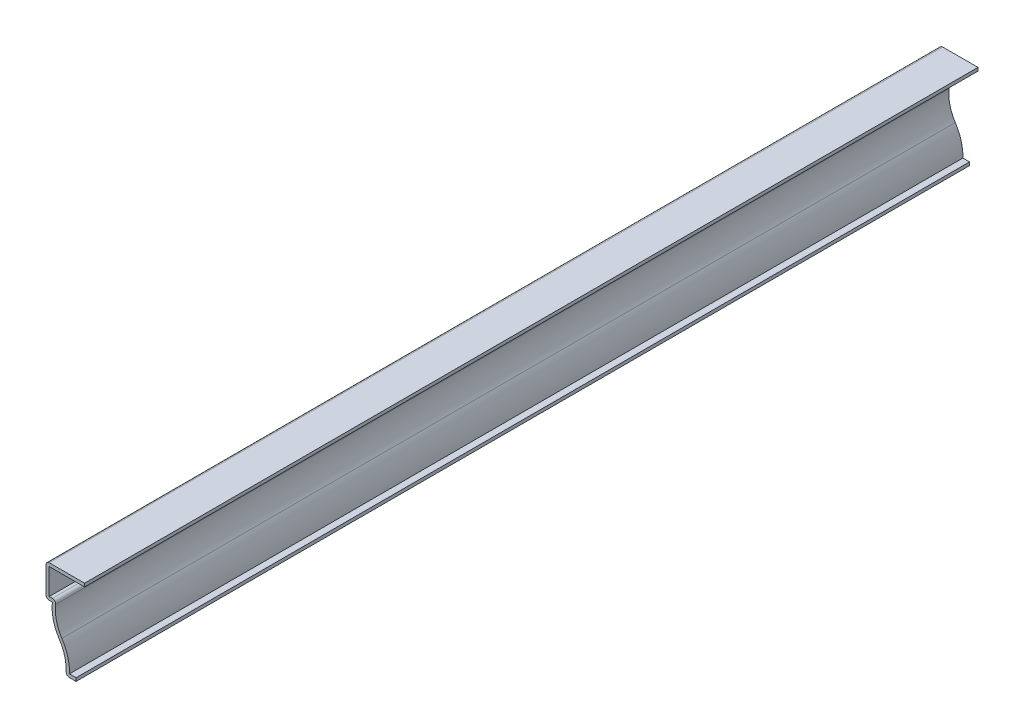
SolidWorks part; units mm, degrees
ref_plane "Front Plane" through (0, 0, 0) normal (0, 0, 1) x (1, 0, 0)
ref_plane "Top Plane" through (0, 0, 0) normal (0, 1, 0) x (1, 0, 0)
ref_plane "Right Plane" through (0, 0, 0) normal (1, 0, 0) x (0, 0, -1)
sketch "Sketch1" plane through (0, 0, 0) normal (0, 0, 1) x (1, 0, 0)
  line L0 (0, 0) -> (0, 34.925) construction
  line L1 (0, 34.925) -> (-15.0812, 34.925)
  line L2 (-15.0812, 34.925) -> (-15.0813, 22.225)
  line L3 (-15.0813, 22.225) -> (-12.5892, 22.225)
  line L4 (-7.2818, 0) -> (-3.313, 0)
  line L5 (-3.313, 0) -> (0, 0) construction
  line L6 (-13.8112, 34.925) -> (-13.8112, 22.225) construction
  line L9 (-15.0813, 22.225) -> (-15.0813, 0) construction
  line L10 (-7.2818, 0) -> (-15.0813, 0) construction
  arc A0 (-12.5892, 22.225) -> (-9.9355, 11.1125) centre (3.9688, 20.306) ccw
  arc A1 (-9.9355, 11.1125) -> (-7.2818, 0) centre (-23.8397, 1.919) cw
  point P11 (-3.313, 17.9522)
  point P12 (-13.5962, 22.225)
  point P13 (-13.8352, 22.225)
  point P15 (-15.0812, 11.1125)
  point P16 (-13.6318, 17.6418)
  point P17 (-12.7, 22.225)
  point P18 (-13.6318, 17.6442)
  point P19 (-10.4095, 11.1125)
  point P20 (-28.3255, 4.309)
  point P21 (-10.0473, 12.6765)
  point P22 (0, 0)
  point P23 (-12.5273, 22.225)
  point P26 (-9.9309, 11.1125)
  dimension "D6" = 1.27
  dimension "D9" = 16.6687
  dimension "D1" = 34.925
  dimension "D2" = 15.0812
  dimension "D3" = 2.3813
  dimension "D4" = 3.9688
  dimension "D5" = 3.313
  dimension "D7" = 22.225
  dimension "D8" = 12.7
extrude "Extrude-Thin1" add sketch "Sketch1" against normal blind 349.25 thin thin type one direction reverse wall 1.27
fillet "Fillet1" radius 1.27 4 edges at (-7.2818, 0, -174.625) (-15.0813, 22.225, -174.625) (-11.0962, 23.495, -174.625) (-15.0812, 34.925, -174.625)
